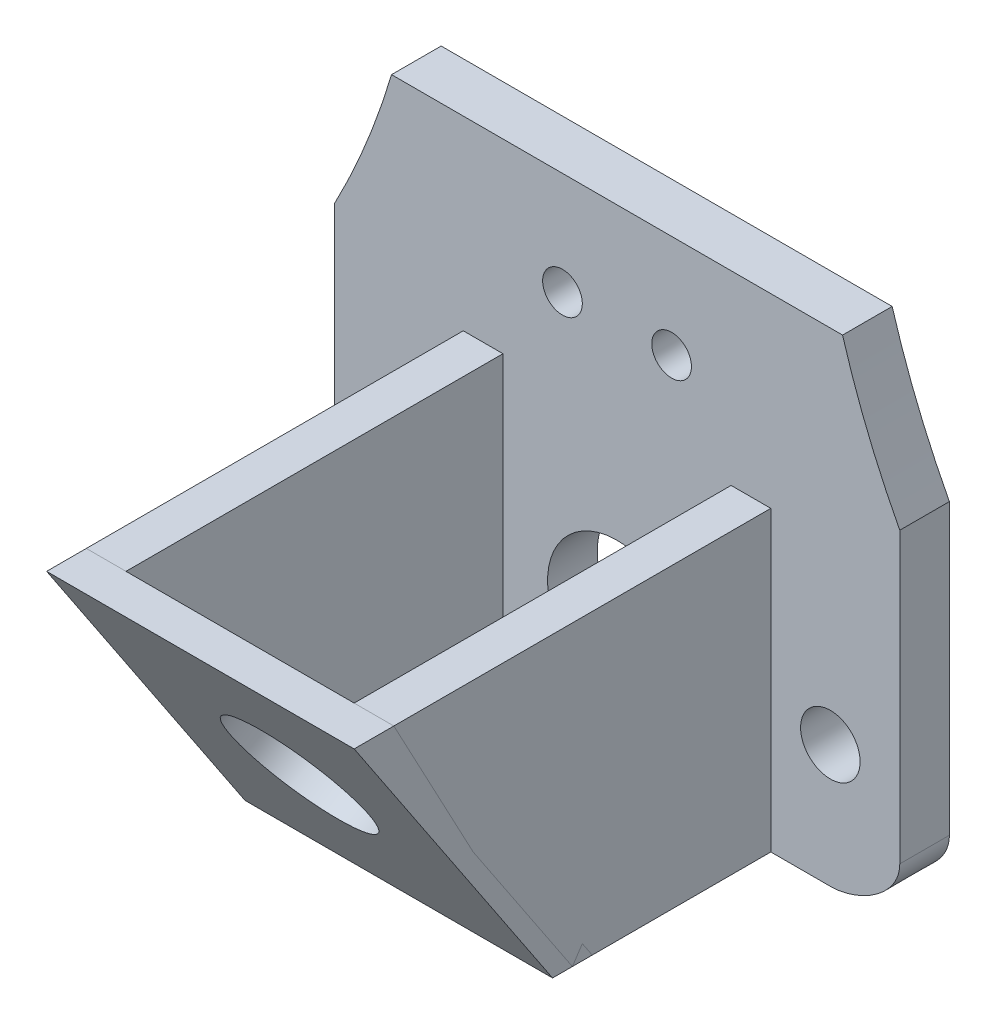
SolidWorks part; units mm, degrees
ref_plane "前视基准面" through (0, 0, 0) normal (0, 0, 1) x (1, 0, 0)
ref_plane "上视基准面" through (0, 0, 0) normal (0, 1, 0) x (1, 0, 0)
ref_plane "右视基准面" through (0, 0, 0) normal (1, 0, 0) x (0, 0, -1)
sketch "Model" plane through (0, 0, 0) normal (0, 0, 1) x (1, 0, 0)
  line L0 (14.6865, 106.179) -> (14.6865, 84.179)
  line L1 (25.1865, 15.9481) -> (35.9365, 15.9481)
  line L2 (35.6865, 106.179) -> (35.6865, 84.179)
  line L3 (39.4365, 80.679) -> (39.4365, 22.179)
  line L4 (39.4365, 22.179) -> (39.4365, 18.679)
  line L5 (25.1865, 15.9481) -> (14.4365, 15.9481)
  line L6 (10.9365, 80.679) -> (10.9365, 22.179)
  line L7 (10.9365, 22.179) -> (10.9365, 18.679)
  line L8 (14.6865, 106.179) -> (35.6865, 106.179)
  circle A0 centre (14.4365, 22.1327) radius 1.5
  circle A1 centre (35.9365, 22.1327) radius 1.5
  circle A2 centre (35.9365, 80.679) radius 1.5
  circle A3 centre (14.4365, 80.679) radius 1.5
  circle A4 centre (25.1865, 25.179) radius 5
  circle A5 centre (27.9365, 35.1327) radius 1
  circle A6 centre (22.4365, 35.1327) radius 1
  spline S0 degree 3 poles (39.4365, 18.679) (39.4365, 17.1993) (37.4163, 15.9481) (35.9365, 15.9481) knots 0 0 0 0 4.439373 4.439373 4.439373 4.439373
  spline S1 degree 3 poles (35.6865, 84.179) (38.1559, 84.179) (39.4365, 82.3889) (39.4365, 80.679) knots 0 0 0 0 5.129571 5.129571 5.129571 5.129571
  spline S2 degree 3 poles (10.9365, 18.679) (10.9365, 17.1993) (12.9567, 15.9481) (14.4365, 15.9481) knots 0 0 0 0 4.439373 4.439373 4.439373 4.439373
  spline S3 degree 3 poles (14.6865, 84.179) (12.2171, 84.179) (10.9365, 82.3889) (10.9365, 80.679) knots 0 0 0 0 5.129571 5.129571 5.129571 5.129571
  point P18 (0, 0)
extrude "凸台-拉伸1" add sketch "Model" along normal blind 2.5
sketch "草图2" plane through (0, 0, 2.5) normal (0, 0, 1) x (1, 0, 0)
  line L0 (14.6865, 106.179) -> (35.6865, 106.179)
  line L2 (35.6865, 106.179) -> (35.6865, 84.179)
  line L3 (15.6865, 105.0116) -> (34.6865, 105.0116)
  line L4 (34.6865, 105.0116) -> (34.6865, 85.9908)
  line L5 (34.6865, 85.9908) -> (15.6865, 85.9908)
  line L6 (15.6865, 85.9908) -> (15.6865, 105.0116)
  line L7 (35.6865, 84.179) -> (14.6865, 84.179)
  line L8 (14.6865, 84.179) -> (14.6865, 106.179)
extrude "凸台-拉伸2" add sketch "草图2" along normal blind 7
sketch "草图3" plane through (0, 0, 2.5) normal (0, 0, 1) x (1, 0, 0)
  line L0 (14.6865, 84.179) -> (35.6865, 84.179) construction
  line L2 (19.3701, 84.179) -> (20.8701, 84.179)
  line L3 (19.3701, 84.179) -> (19.3701, 79.179)
  line L4 (19.3701, 79.179) -> (20.8701, 79.179)
  line L5 (20.8701, 84.179) -> (20.8701, 79.179)
extrude "凸台-拉伸3" add sketch "草图3" along normal blind 7
sketch "草图4" plane through (19.3701, 0, 0) normal (-1, 0, 0) x (0, 0, 1)
  line L0 (9.5, 84.179) -> (2.5, 79.179)
  line L1 (2.5, 80.679) -> (2.5, 18.679) construction
  line L2 (9.5, 79.179) -> (2.5, 79.179) construction
  line L3 (2.5, 79.179) -> (9.5, 79.179)
  line L4 (9.5, 79.179) -> (9.5, 84.179)
extrude "切除-拉伸2" cut sketch "草图4" against normal blind 7
sketch3d "3D草图1"
  line L2 (20.8701, 84.179, 2.5) -> (35.6865, 84.179, 2.5) construction
  line L4 (31.0065, 84.179, 2.5) -> (29.5065, 84.179, 2.5)
  line L5 (31.0065, 84.179, 2.5) -> (31.0065, 79.179, 2.5)
  line L6 (31.0065, 79.179, 2.5) -> (29.5065, 79.179, 2.5)
  line L7 (29.5065, 84.179, 2.5) -> (29.5065, 79.179, 2.5)
extrude "凸台-拉伸6" add sketch "3D草图1" along direction (0, 0, 1) on the side against the normal blind 7
sketch "草图12" plane through (29.5065, 0, 0) normal (-1, 0, 0) x (0, 0, 1)
  line L0 (9.5, 84.179) -> (9.5, 79.179)
  line L1 (9.5, 79.179) -> (2.5, 79.179)
  line L2 (2.5, 79.179) -> (9.5, 84.179)
extrude "切除-拉伸4" cut sketch "草图12" against normal blind 7
sketch "草图13" plane through (0, 84.179, 0) normal (0, -1, 0) x (1, 0, 0)
  line L2 (20.8701, 2.5) -> (29.5065, 2.5) construction
  line L4 (24.1865, 2.5) -> (26.1865, 2.5)
  line L5 (24.1865, 2.5) -> (24.1865, 4.5)
  line L6 (24.1865, 4.5) -> (26.1865, 4.5)
  line L7 (26.1865, 2.5) -> (26.1865, 4.5)
extrude "切除-拉伸5" cut sketch "草图13" against normal blind 7
sketch "草图14" plane through (0, 0, 2.5) normal (0, 0, 1) x (1, 0, 0)
  line L0 (19.4365, 30.9481) -> (19.4365, 17.9481)
  line L1 (14.4365, 15.9481) -> (35.9365, 15.9481) construction
  line L2 (17.4365, 15.9481) -> (17.4365, 30.9481)
  line L3 (17.4365, 30.9481) -> (19.4365, 30.9481)
  line L6 (32.9365, 15.9481) -> (32.9365, 30.9481)
  line L7 (32.9365, 30.9481) -> (30.9365, 30.9481)
  line L12 (30.9365, 30.9481) -> (30.9365, 17.9481)
  line L13 (30.9365, 17.9481) -> (19.4365, 17.9481)
  line L14 (17.4365, 15.9481) -> (32.9365, 15.9481)
extrude "凸台-拉伸7" add sketch "草图14" along normal blind 20
sketch "草图15" plane through (17.4365, 0, 0) normal (-1, 0, 0) x (0, 0, 1)
  line L1 (22.5, 30.9481) -> (22.5, 15.9481)
  line L2 (22.5, 15.9481) -> (12.5, 15.9481)
  line L3 (22.5, 15.9481) -> (2.5, 15.9481) construction
  line L4 (12.5, 15.9481) -> (22.5, 30.9481)
extrude "切除-拉伸6" cut sketch "草图15" against normal blind 20
sketch "草图16" plane through (0, -0.8621, 1.2932) normal (0, -0.5547, 0.8321) x (1, 0, 0)
sketch "草图19" plane through (0, -0.8621, 1.2932) normal (0, -0.5547, 0.8321) x (1, 0, 0)
  line L17 (32.9365, 38.2311) -> (30.9365, 38.2311)
  line L18 (30.9365, 38.2311) -> (30.9365, 22.6071)
  line L19 (30.9365, 22.6071) -> (19.4365, 22.6071)
  line L20 (19.4365, 22.6071) -> (19.4365, 38.2311)
  line L21 (19.4365, 38.2311) -> (17.4365, 38.2311)
  line L22 (17.4365, 38.2311) -> (17.4365, 20.2034)
  line L23 (17.4365, 20.2034) -> (32.9365, 20.2034)
  line L24 (32.9365, 20.2034) -> (32.9365, 38.2311)
  line L25 (32.9365, 38.2311) -> (30.9365, 38.2311)
  line L30 (17.4365, 38.2311) -> (17.4365, 20.2034)
  line L31 (17.4365, 20.2034) -> (32.9365, 20.2034)
  line L32 (32.9365, 20.2034) -> (32.9365, 38.2311)
  dimension "D1" = 0
sketch "草图20" plane through (0, -0.8621, 1.2932) normal (0, -0.5547, 0.8321) x (1, 0, 0)
  line L0 (17.4365, 38.2311) -> (32.9365, 38.2311)
  line L1 (32.9365, 38.2311) -> (32.9365, 20.2034)
  line L2 (32.9365, 20.2034) -> (17.4365, 20.2034)
  line L3 (17.4365, 20.2034) -> (17.4365, 38.2311)
extrude "凸台-拉伸9" add sketch "草图20" along direction (0, 0, -1) on the side against the normal mid plane 2 separate body
sketch "草图21" plane through (0, -1.3237, 1.9855) normal (0, -0.5547, 0.8321) x (1, 0, 0)
  circle A0 centre (25.1865, 29.772) radius 3.5
extrude "切除-拉伸7" cut sketch "草图21" against normal blind 2
sketch "草图22" plane through (0, 0, 2.5) normal (0, 0, 1) x (1, 0, 0)
sketch "草图23" plane through (0, 0, 2.5) normal (0, 0, 1) x (1, 0, 0)
  circle A0 centre (25.1865, 22.179) radius 3.5
extrude "切除-拉伸8" cut sketch "草图23" against normal blind 4
sketch "草图25" plane through (0, 0, 2.5) normal (0, 0, 1) x (1, 0, 0)
  line L1 (25.1865, 73.429) -> (26.2145, 73.429)
  line L2 (26.2145, 73.429) -> (26.2145, 60.429)
  line L3 (26.2145, 60.429) -> (24.1865, 60.429)
  line L4 (24.1865, 60.429) -> (24.1865, 73.429)
  line L5 (24.1865, 73.429) -> (25.1865, 73.429)
  line L7 (30.1865, 73.429) -> (33.1865, 73.429)
  line L8 (33.1865, 73.429) -> (33.1865, 60.429)
  line L11 (30.1865, 73.429) -> (30.1865, 60.429)
  line L12 (30.1865, 60.429) -> (33.1865, 60.429)
  line L13 (20.1865, 60.429) -> (17.1865, 60.429)
  line L14 (17.1865, 73.429) -> (17.1865, 60.429)
  line L15 (20.1865, 73.429) -> (17.1865, 73.429)
  line L16 (20.1865, 73.429) -> (20.1865, 60.429)
extrude "凸台-拉伸10" add sketch "草图25" along normal blind 15
sketch "草图26" plane through (17.1865, 0, 0) normal (-1, 0, 0) x (0, 0, 1)
  circle A0 centre (11, 66.929) radius 2.5
extrude "切除-拉伸9" cut sketch "草图26" against normal blind 18
sketch "草图27" plane through (17.1865, 0, 0) normal (-1, 0, 0) x (0, 0, 1)
  line L0 (17.5, 73.429) -> (2.5, 73.429) construction
  line L1 (11, 73.429) -> (11, 75.5365)
  line L2 (11, 75.5365) -> (21.7471, 75.5365)
  line L3 (21.7471, 75.5365) -> (21.7471, 59.0459)
  line L4 (21.7471, 59.0459) -> (11, 59.4314)
  line L5 (11, 59.4314) -> (11, 60.429)
  arc A0 (11, 73.429) -> (11, 60.429) centre (11, 66.929) cw
extrude "切除-拉伸10" cut sketch "草图27" against normal blind 16
sketch "草图28" plane through (0, 84.179, 0) normal (0, -1, 0) x (1, 0, 0)
  line L1 (14.4365, 2.5) -> (17.4365, 2.5) construction
  line L2 (16.6865, 2.5) -> (16.6865, 4.5)
  line L3 (16.6865, 4.5) -> (19.3701, 4.5)
  line L4 (19.3701, 4.5) -> (19.3701, 2.5)
  line L5 (17.4365, 2.5) -> (19.4365, 2.5) construction
  line L6 (14.6865, 2.5) -> (19.3701, 2.5) construction
  line L7 (19.3701, 2.5) -> (16.6865, 2.5)
  line L11 (31.0014, 2.4958) -> (33.6851, 2.4938)
  line L12 (31.0029, 4.4958) -> (31.0014, 2.4958)
  line L13 (33.6851, 2.4938) -> (33.6865, 4.4938)
  line L14 (33.6865, 4.4938) -> (31.0029, 4.4958)
  line L15 (31.0029, 4.4958) -> (33.6865, 4.4938)
  line L16 (33.6851, 2.4938) -> (31.0014, 2.4958)
sketch "草图29" plane through (0, 84.179, 0) normal (0, -1, 0) x (1, 0, 0)
extrude "切除-拉伸12" cut sketch "草图28" against normal blind 2 contours L3 L4 L7 L2 | L14 L12 L11 L13
sketch "草图30" plane through (0, 0, 2.5) normal (0, 0, 1) x (1, 0, 0)
  circle A0 centre (28.1883, 55.179) radius 1
  circle A2 centre (22.1883, 54.179) radius 1
extrude "切除-拉伸13" cut sketch "草图30" against normal blind 10
sketch "草图31" plane through (0, 0, 2.5) normal (0, 0, 1) x (1, 0, 0)
  circle A0 centre (-23.5635, 51.429) radius 39
  circle A1 centre (73.9365, 51.429) radius 39
extrude "切除-拉伸14" cut sketch "草图31" against normal blind 10
sketch "草图32" plane through (0, 0, 2.5) normal (0, 0, 1) x (1, 0, 0)
  line L0 (17.2145, 60.429) -> (15.2974, 47.8229)
  line L5 (33.1865, 60.429) -> (35.1036, 47.8229)
  arc A1 (39.4365, 69.6156) -> (39.4365, 33.2425) centre (73.9365, 51.429) ccw construction
  spline S0 degree 3 poles (33.1865, 60.429) (33.9982, 57.2618) (34.5214, 55.0305) (44.3629, 53.3009) (47.8, 54.5625) (47.6334, 53.0148) (45.2472, 51.1375) (41.1508, 48.687) (40.6479, 48.5267) (35.1036, 47.8229) knots 0 0 0 0 0.228684 0.270207 0.399122 0.431668 0.563126 0.621603 1 1 1 1
  spline S1 degree 3 poles (17.2145, 60.429) (16.4028, 57.2618) (15.8796, 55.0305) (6.0382, 53.3009) (2.601, 54.5625) (2.7677, 53.0148) (5.1538, 51.1375) (9.2503, 48.687) (9.7531, 48.5267) (15.2974, 47.8229) knots 0 0 0 0 0.228684 0.270207 0.399122 0.431668 0.563126 0.621603 1 1 1 1
sketch "草图33" plane through (0, 0, 2.5) normal (0, 0, 1) x (1, 0, 0)
  circle A0 centre (22.4365, 35.1327) radius 1
  circle A1 centre (27.9365, 35.1327) radius 1
extrude "切除-拉伸15" cut sketch "草图33" against normal blind 2.5
extrude "凸台-拉伸13" add sketch "草图32" against normal blind 2.5
sketch "草图34" plane through (0, 0, 2.5) normal (0, 0, 1) x (1, 0, 0)
  line L0 (13.8212, 40.3211) -> (36.5523, 40.3194)
  line L1 (36.5523, 40.3194) -> (46.0821, 32.1327)
  line L2 (46.0821, 32.1327) -> (58.9144, 113.0926)
  line L3 (58.9144, 113.0926) -> (0, 109.1262)
  line L4 (0, 109.1262) -> (-4.0804, 42.2818)
  line L5 (-4.0804, 42.2818) -> (13.8212, 40.3211)
  arc A0 (10.9365, 33.2425) -> (15.2698, 47.8264) centre (-23.5635, 51.429) ccw construction
  arc A1 (35.1036, 47.8229) -> (39.4365, 33.2425) centre (73.9365, 51.429) ccw construction
extrude "切除-拉伸16" cut sketch "草图34" against normal mid plane 81
